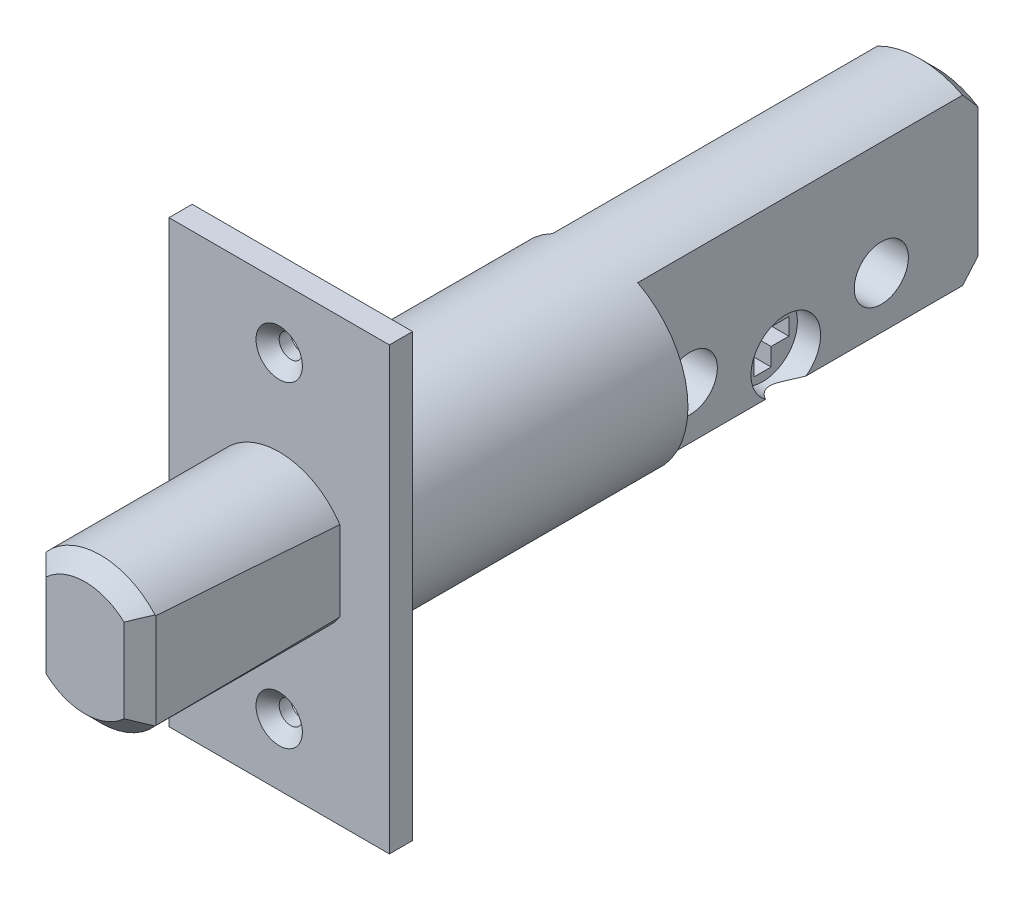
SolidWorks part; units mm, degrees
ref_plane "Front Plane" through (0, 0, 0) normal (0, 0, 1) x (1, 0, 0)
ref_plane "Top Plane" through (0, 0, 0) normal (0, 1, 0) x (1, 0, 0)
ref_plane "Right Plane" through (0, 0, 0) normal (1, 0, 0) x (0, 0, -1)
sketch "Sketch2" plane through (0, 0, 0) normal (0, 0, 1) x (1, 0, 0)
  circle A0 centre (0, 0) radius 12
  dimension "D1" = 24
extrude "Boss-Extrude1" add sketch "Sketch2" against normal blind 81.85
sketch "Sketch3" plane through (0, 0, 0) normal (0, 0, 1) x (1, 0, 0)
  line L1 (-14.25, 28.5) -> (14.25, 28.5)
  line L2 (-14.25, 28.5) -> (-14.25, -28.5)
  line L3 (-14.25, -28.5) -> (14.25, -28.5)
  line L4 (14.25, 28.5) -> (14.25, -28.5)
  circle A0 centre (0, 20.5) radius 1.5
  circle A1 centre (0, -20.5) radius 1.5
  circle A2 centre (0, 0) radius 12 construction
  dimension "D5" = 41
  dimension "D6" = 20.5
  dimension "D7" = 3
  dimension "D8" = 3
  dimension "D1" = 28.5
  dimension "D2" = 14.25
  dimension "D3" = 57
  dimension "D4" = 28.5
extrude "Boss-Extrude2" add sketch "Sketch3" along normal blind 3
chamfer "Chamfer1" distance 1.5 angle 45 2 edges at (1.5, -20.5, 3) (1.5, 20.5, 3)
sketch "Sketch4" plane through (0, 0, 3) normal (0, 0, 1) x (1, 0, 0)
  circle A0 centre (0, 0) radius 9.4
  dimension "D1" = 18.8
extrude "Boss-Extrude3" add sketch "Sketch4" along normal blind 25.1
sketch "Sketch5" plane through (0, 0, 0) normal (0, 1, 0) x (1, 0, 0)
  line L0 (0, -28.1) -> (-7.05, -28.1) construction
  line L1 (-9.4, -28.1) -> (9.4, -28.1) construction
  line L7 (0, -28.1) -> (0, 0) construction
  line L8 (0, -3) -> (-7.85, -3) construction
  line L9 (14.25, -3) -> (-14.25, -3) construction
  line L10 (-9.4, -3) -> (9.4, -3) construction
  line L11 (-7.85, -3) -> (-7.05, -28.1)
  line L12 (-9.4, -28.1) -> (-9.4, -3)
  line L13 (-9.4, -3) -> (-7.85, -3)
  line L14 (-9.4, -28.1) -> (-7.05, -28.1)
  line L15 (9.4, -3) -> (7.85, -3)
  line L16 (9.4, -28.1) -> (9.4, -3)
  line L17 (7.85, -3) -> (7.05, -28.1)
  line L18 (9.4, -28.1) -> (7.05, -28.1)
  dimension "D1" = 7.85
  dimension "D2" = 7.05
extrude "Cut-Extrude1" cut sketch "Sketch5" against normal through all both and the other way through all
chamfer "Chamfer2" distance 2 angle 45 4 edges at (0, -9.4, 28.1) (0, 9.4, 28.1) (7.05, 0, 28.1) (-7.05, 0, 28.1)
chamfer "Chamfer3" distance 2 angle 45 1 edges at (12, 0, -81.85)
sketch "Sketch6" plane through (0, 0, 0) normal (1, 0, 0) x (0, 0, -1)
  line L0 (-3, -28.5) -> (-3, 28.5) construction
  line L1 (0, 0) -> (81.85, 0) construction
  line L2 (81.85, -10) -> (81.85, 10) construction
  circle A0 centre (57, -7) radius 4.5
  dimension "D2" = 7
  dimension "D3" = 9
  dimension "D1" = 60
extrude "Cut-Extrude2" cut sketch "Sketch6" against normal through all both and the other way through all
sketch "Sketch7" plane through (0, 0, -81.85) normal (0, 0, -1) x (-1, 0, 0)
  line L1 (-5.5, 15) -> (5.5, 15)
  line L2 (-5.5, 15) -> (-5.5, -15)
  line L3 (-5.5, -15) -> (5.5, -15)
  line L4 (5.5, 15) -> (5.5, -15)
  line L5 (-17.0316, 21.9897) -> (18.6212, 21.9897)
  line L6 (-17.0316, 21.9897) -> (-17.0316, -21.3085)
  line L7 (-17.0316, -21.3085) -> (18.6212, -21.3085)
  line L8 (18.6212, 21.9897) -> (18.6212, -21.3085)
  dimension "D1" = 11
  dimension "D2" = 5.5
  dimension "D3" = 30
  dimension "D4" = 15
extrude "Cut-Extrude3" cut sketch "Sketch7" against normal blind 44
sketch "Sketch8" plane through (0, 0, 0) normal (1, 0, 0) x (0, 0, -1)
  line L1 (55.9, -3.6) -> (58.1, -3.6)
  line L2 (55.9, -3.6) -> (55.9, -10.4)
  line L3 (55.9, -10.4) -> (58.1, -10.4)
  line L4 (58.1, -3.6) -> (58.1, -10.4)
  line L5 (53.6, -5.9) -> (60.4, -5.9)
  line L6 (53.6, -5.9) -> (53.6, -8.1)
  line L7 (53.6, -8.1) -> (60.4, -8.1)
  line L8 (60.4, -5.9) -> (60.4, -8.1)
  circle A0 centre (57, -7) radius 4.5
  dimension "D1" = 9
  dimension "D2" = 2.2
  dimension "D3" = 6.8
  dimension "D4" = 2.2
  dimension "D5" = 6.8
  dimension "D6" = 1.1
  dimension "D7" = 3.4
  dimension "D8" = 3.4
  dimension "D9" = 1.1
extrude "Boss-Extrude4" add sketch "Sketch8" along normal blind 2.5 and the other way blind 2.5 contours A0 L5 L8 L7 L4 L3 L2 L6 L1
sketch "Sketch9" plane through (5.5, 0, 0) normal (1, 0, 0) x (0, 0, -1)
  circle A0 centre (44.65, -4) radius 3.5
  circle A1 centre (69.35, -4) radius 3.5
  circle A2 centre (57, -7) radius 4.5 construction
  arc A3 (59.6106, -10.6654) -> (54.3894, -10.6654) centre (57, -7) ccw construction
  dimension "D1" = 7
  dimension "D2" = 7
  dimension "D3" = 24.7
  dimension "D4" = 12.35
  dimension "D5" = 3
extrude "Cut-Extrude4" cut sketch "Sketch9" against normal through all
